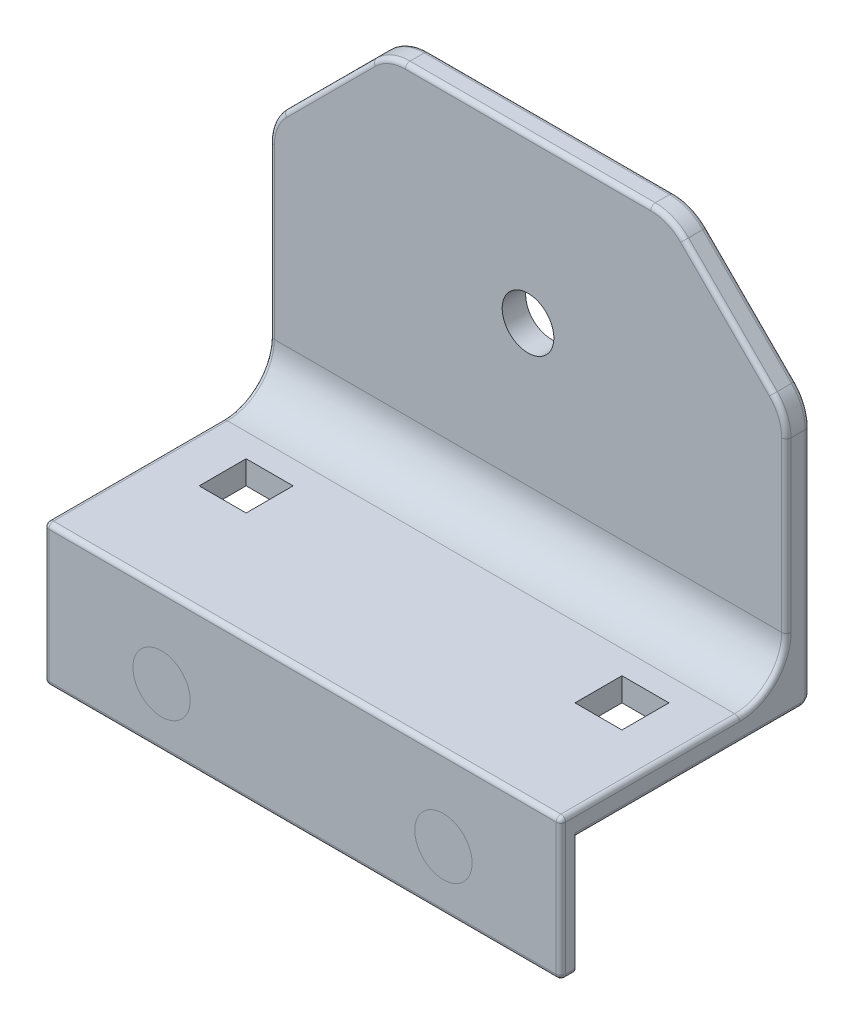
SolidWorks part; units mm, degrees
ref_plane "Front Plane" through (0, 0, 0) normal (0, 0, 1) x (1, 0, 0)
ref_plane "Top Plane" through (0, 0, 0) normal (0, 1, 0) x (1, 0, 0)
ref_plane "Right Plane" through (0, 0, 0) normal (1, 0, 0) x (0, 0, -1)
sketch "Sketch1" plane through (0, 0, 0) normal (0, 1, 0) x (1, 0, 0)
  line L1 (0, 0) -> (110, 0)
  line L2 (0, 0) -> (0, 50)
  line L3 (0, 50) -> (110, 50)
  line L4 (110, 0) -> (110, 50)
  line L5 (10, 30) -> (20, 30)
  line L6 (10, 30) -> (10, 20)
  line L7 (10, 20) -> (20, 20)
  line L8 (20, 30) -> (20, 20)
  line L9 (90, 30) -> (100, 30)
  line L10 (90, 30) -> (90, 20)
  line L11 (90, 20) -> (100, 20)
  line L12 (100, 30) -> (100, 20)
  dimension "D1" = 110
  dimension "D2" = 10
  dimension "D3" = 10
  dimension "D4" = 10
  dimension "D5" = 10
  dimension "D6" = 50
  dimension "D7" = 20
  dimension "D8" = 20
  dimension "D9" = 10
  dimension "D10" = 70
extrude "Boss-Extrude1" add sketch "Sketch1" along normal blind 5
sketch "Sketch2" plane through (0, 0, 0) normal (0, 0, 1) x (1, 0, 0)
  line L0 (0, -25) -> (25, -25)
  line L1 (0, 5) -> (110, 5)
  line L2 (0, 5) -> (0, -25)
  line L3 (0, -25) -> (110, -25)
  line L4 (110, 5) -> (110, -25)
  line L5 (110, -25) -> (85, -25)
  line L6 (109, -25) -> (1, -25) construction
  circle A0 centre (25, -12.5) radius 6.1
  circle A1 centre (85, -12.5) radius 6.1
  line M3 (0, 0) -> (110, 0)
  line M4 (110, 0) -> (110, 5)
  line M5 (110, 5) -> (0, 5)
  line M6 (0, 5) -> (0, 0)
  dimension "D4" = 12.2
  dimension "D5" = 12.2
  dimension "D1" = 30
  dimension "D2" = 25
  dimension "D3" = 25
extrude "Boss-Extrude2" add sketch "Sketch2" along normal blind 3 contours L4 L2 L0 L3 A1 A0 M3 | M6 M3 M4 M5
sketch "Sketch3" plane through (0, 0, -50) normal (0, 0, -1) x (-1, 0, 0)
  line L0 (-110, 5) -> (0, 5)
  line L1 (0, 5) -> (0, 55)
  line L2 (0, 55) -> (-110, 55)
  line L3 (-110, 55) -> (-110, 5)
  line L4 (-110, 55) -> (-110, 45)
  line L5 (-110, 55) -> (-85.2513, 79.7487)
  line L6 (-85.2513, 79.7487) -> (-24.7487, 79.7487)
  line L7 (-24.7487, 79.7487) -> (0, 55)
  circle A2 centre (-55, 45) radius 5.5
  line M4 (0, 5) -> (-110, 5)
  dimension "D3" = 11
  dimension "D1" = 50
  dimension "D2" = 10
  dimension "D4" = 45
  dimension "D5" = 45
  dimension "D6" = 35
extrude "Boss-Extrude3" add sketch "Sketch3" against normal blind 5 contours L2 L3 L1 M4 | L7 L6 L5 L2
fillet "Fillet1" radius 10 4 edges at (85.2513, 79.7487, -47.5) (110, 55, -47.5) (0, 55, -47.5) (24.7487, 79.7487, -47.5)
fillet "Fillet2" radius 10 1 edges at (55, 5, -45)
fillet "Fillet3" radius 2 1 edges at (55, 0, -50)
fillet "Fillet4" radius 1 26 edges at (110, 0, -24) (110, 0.5858, -49.4142) (110, 26.4289, -50) (109.2388, 54.6847, -50) (97.6256, 67.3744, -50) (84.936, 78.9875, -50) (0, 0, -24) (0, 0.5858, -49.4142) (0, 26.4289, -50) (0.7612, 54.6847, -50) (12.3744, 67.3744, -50) (25.064, 78.9875, -50) (110, 5, -16) (110, 7.9289, -42.0711) (110, 32.9289, -45) (109.2388, 54.6847, -45) (97.6256, 67.3744, -45) (84.936, 78.9875, -45) (0, 5, -16) (0, 7.9289, -42.0711) (0, 32.9289, -45) (0.7612, 54.6847, -45) (12.3744, 67.3744, -45) (25.064, 78.9875, -45) (55, 79.7487, -50) (55, 79.7487, -45)
fillet "Fillet5" radius 1 9 edges at (110, -10.5, 3) (109.7071, 4.7071, 3) (0, -10.5, 3) (0.2929, 4.7071, 3) (55, -25, 0) (55, -25, 3) (55, 5, 3) (110, -25, 1.5) (0, -25, 1.5)
sketch "Sketch4" plane through (0, 0, 3) normal (0, 0, 1) x (1, 0, 0)
  circle A0 centre (25, -12.5) radius 6.1
  circle A1 centre (85, -12.5) radius 6.1
extrude "Boss-Extrude4" add sketch "Sketch4" against normal blind 3 separate body
